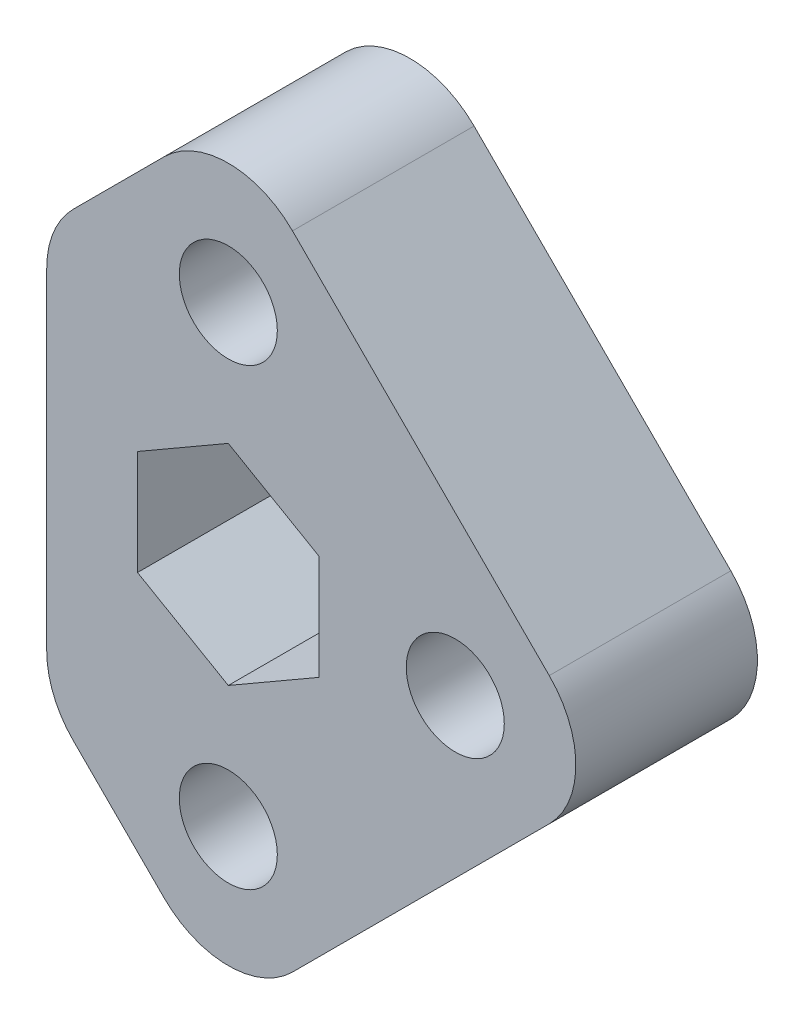
SolidWorks part; units mm, degrees
ref_plane "Front Plane" through (0, 0, 0) normal (0, 0, 1) x (1, 0, 0)
ref_plane "Top Plane" through (0, 0, 0) normal (0, 1, 0) x (1, 0, 0)
ref_plane "Right Plane" through (0, 0, 0) normal (1, 0, 0) x (0, 0, -1)
sketch "Sketch2" plane through (0, 0, 0) normal (0, 0, 1) x (1, 0, 0)
  line L0 (0, -55) -> (0, 55) construction
  line L1 (6.35, 3.6662) -> (0, 7.3323)
  line L2 (0, 7.3323) -> (-6.35, 3.6662)
  line L3 (-6.35, 3.6662) -> (-6.35, -3.6662)
  line L4 (-6.35, -3.6662) -> (0, -7.3323)
  line L5 (0, -7.3323) -> (6.35, -3.6662)
  line L6 (6.35, -3.6662) -> (6.35, 3.6662)
  line L7 (0, 0) -> (0, 15.875) construction
  line L8 (-4.4901, 22.4506) -> (-10.8401, 16.1006)
  line L9 (55, 0) -> (-55, 0) construction
  line L10 (-10.8401, -16.1006) -> (-4.4901, -22.4506)
  line L11 (4.4901, -22.4506) -> (22.4506, -4.4901)
  line L12 (22.4506, 4.4901) -> (4.4901, 22.4506)
  line L13 (0, 26.9408) -> (0, -26.9408) construction
  line L15 (-12.7, 11.6105) -> (-12.7, -11.6105)
  line L16 (-15.875, 0) -> (26.9408, 0) construction
  circle A0 centre (0, 0) radius 6.35 construction
  circle A1 centre (0, 15.875) radius 3.429
  circle A2 centre (15.875, 0) radius 3.429
  circle A3 centre (0, -15.875) radius 3.429
  circle A6 centre (0, 0) radius 15.875 construction
  arc A8 (-4.4901, -22.4506) -> (4.4901, -22.4506) centre (0, -17.9605) ccw
  arc A9 (22.4506, -4.4901) -> (22.4506, 4.4901) centre (17.9605, 0) ccw
  arc A10 (4.4901, 22.4506) -> (-4.4901, 22.4506) centre (0, 17.9605) ccw
  circle A11 centre (-15.875, 0) radius 3.429 [skipped]
  arc A12 (-12.7, -11.6105) -> (-10.8401, -16.1006) centre (-6.35, -11.6105) ccw
  arc A13 (-12.7, 11.6105) -> (-10.8401, 16.1006) centre (-6.35, 11.6105) cw
  point P14 (0, 0)
  dimension "D1" = 12.7
  dimension "D3" = 12.7
  dimension "D4" = 6.858
  dimension "D6" = 38.1
  dimension "D7" = 6.35
  dimension "D2" = 31.75
  dimension "D5" = 4
extrude "Boss-Extrude1" add sketch "Sketch2" along normal blind 12.7
